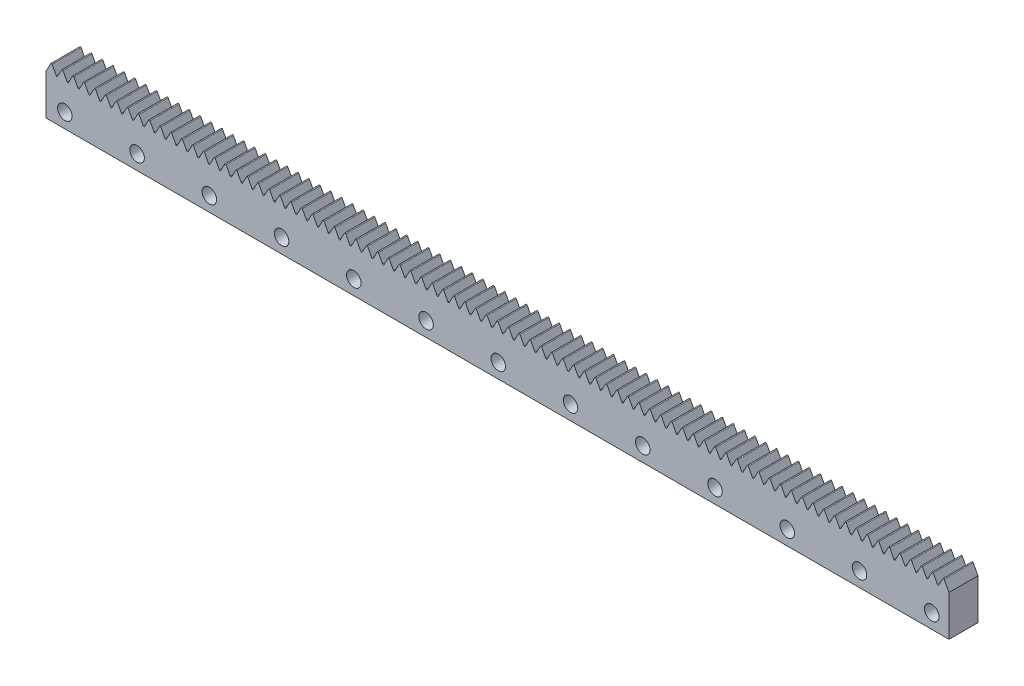
SolidWorks part; units mm, degrees
ref_plane "Front Plane" through (0, 0, 0) normal (0, 0, 1) x (1, 0, 0)
ref_plane "Top Plane" through (0, 0, 0) normal (0, 1, 0) x (1, 0, 0)
ref_plane "Right Plane" through (0, 0, 0) normal (1, 0, 0) x (0, 0, -1)
sketch "Sketch1" plane through (0, 0, 0) normal (0, 0, 1) x (1, 0, 0)
  line L0 (0, 0) -> (124.5, 0)
  line L1 (124.5, 0) -> (124.5, 5.6)
  line L2 (0, 0) -> (0, 5.6)
  line L19 (123.8381, 6.8355) -> (124.5, 5.6)
  line L20 (123.6619, 6.8355) -> (123.0881, 5.7645)
  line L21 (122.3381, 6.8355) -> (122.9119, 5.7645)
  line L22 (122.1619, 6.8355) -> (121.5881, 5.7645)
  line L23 (120.8381, 6.8355) -> (121.4119, 5.7645)
  line L24 (120.6619, 6.8355) -> (120.0881, 5.7645)
  line L25 (119.3381, 6.8355) -> (119.9119, 5.7645)
  line L26 (119.1619, 6.8355) -> (118.5881, 5.7645)
  line L27 (117.8381, 6.8355) -> (118.4119, 5.7645)
  line L28 (117.6619, 6.8355) -> (117.0881, 5.7645)
  line L29 (116.3381, 6.8355) -> (116.9119, 5.7645)
  line L30 (116.1619, 6.8355) -> (115.5881, 5.7645)
  line L31 (114.8381, 6.8355) -> (115.4119, 5.7645)
  line L32 (114.6619, 6.8355) -> (114.0881, 5.7645)
  line L33 (113.3381, 6.8355) -> (113.9119, 5.7645)
  line L34 (113.1619, 6.8355) -> (112.5881, 5.7645)
  line L35 (111.8381, 6.8355) -> (112.4119, 5.7645)
  line L36 (111.6619, 6.8355) -> (111.0881, 5.7645)
  line L37 (110.3381, 6.8355) -> (110.9119, 5.7645)
  line L38 (110.1619, 6.8355) -> (109.5881, 5.7645)
  line L39 (108.8381, 6.8355) -> (109.4119, 5.7645)
  line L40 (108.6619, 6.8355) -> (108.0881, 5.7645)
  line L41 (107.3381, 6.8355) -> (107.9119, 5.7645)
  line L42 (107.1619, 6.8355) -> (106.5881, 5.7645)
  line L43 (105.8381, 6.8355) -> (106.4119, 5.7645)
  line L44 (105.6619, 6.8355) -> (105.0881, 5.7645)
  line L45 (104.3381, 6.8355) -> (104.9119, 5.7645)
  line L46 (104.1619, 6.8355) -> (103.5881, 5.7645)
  line L47 (102.8381, 6.8355) -> (103.4119, 5.7645)
  line L48 (102.6619, 6.8355) -> (102.0881, 5.7645)
  line L49 (101.3381, 6.8355) -> (101.9119, 5.7645)
  line L50 (101.1619, 6.8355) -> (100.5881, 5.7645)
  line L51 (99.8381, 6.8355) -> (100.4119, 5.7645)
  line L52 (99.6619, 6.8355) -> (99.0881, 5.7645)
  line L53 (98.3381, 6.8355) -> (98.9119, 5.7645)
  line L54 (98.1619, 6.8355) -> (97.5881, 5.7645)
  line L55 (96.8381, 6.8355) -> (97.4119, 5.7645)
  line L56 (96.6619, 6.8355) -> (96.0881, 5.7645)
  line L57 (95.3381, 6.8355) -> (95.9119, 5.7645)
  line L58 (95.1619, 6.8355) -> (94.5881, 5.7645)
  line L59 (93.8381, 6.8355) -> (94.4119, 5.7645)
  line L60 (93.6619, 6.8355) -> (93.0881, 5.7645)
  line L61 (92.3381, 6.8355) -> (92.9119, 5.7645)
  line L62 (92.1619, 6.8355) -> (91.5881, 5.7645)
  line L63 (90.8381, 6.8355) -> (91.4119, 5.7645)
  line L64 (90.6619, 6.8355) -> (90.0881, 5.7645)
  line L65 (89.3381, 6.8355) -> (89.9119, 5.7645)
  line L66 (89.1619, 6.8355) -> (88.5881, 5.7645)
  line L67 (87.8381, 6.8355) -> (88.4119, 5.7645)
  line L68 (87.6619, 6.8355) -> (87.0881, 5.7645)
  line L69 (86.3381, 6.8355) -> (86.9119, 5.7645)
  line L70 (86.1619, 6.8355) -> (85.5881, 5.7645)
  line L71 (84.8381, 6.8355) -> (85.4119, 5.7645)
  line L72 (84.6619, 6.8355) -> (84.0881, 5.7645)
  line L73 (83.3381, 6.8355) -> (83.9119, 5.7645)
  line L74 (83.1619, 6.8355) -> (82.5881, 5.7645)
  line L75 (81.8381, 6.8355) -> (82.4119, 5.7645)
  line L76 (81.6619, 6.8355) -> (81.0881, 5.7645)
  line L77 (80.3381, 6.8355) -> (80.9119, 5.7645)
  line L78 (80.1619, 6.8355) -> (79.5881, 5.7645)
  line L79 (78.8381, 6.8355) -> (79.4119, 5.7645)
  line L80 (78.6619, 6.8355) -> (78.0881, 5.7645)
  line L81 (77.3381, 6.8355) -> (77.9119, 5.7645)
  line L82 (77.1619, 6.8355) -> (76.5881, 5.7645)
  line L83 (75.8381, 6.8355) -> (76.4119, 5.7645)
  line L84 (75.6619, 6.8355) -> (75.0881, 5.7645)
  line L85 (74.3381, 6.8355) -> (74.9119, 5.7645)
  line L86 (74.1619, 6.8355) -> (73.5881, 5.7645)
  line L87 (72.8381, 6.8355) -> (73.4119, 5.7645)
  line L88 (72.6619, 6.8355) -> (72.0881, 5.7645)
  line L89 (71.3381, 6.8355) -> (71.9119, 5.7645)
  line L90 (71.1619, 6.8355) -> (70.5881, 5.7645)
  line L91 (69.8381, 6.8355) -> (70.4119, 5.7645)
  line L92 (69.6619, 6.8355) -> (69.0881, 5.7645)
  line L93 (68.3381, 6.8355) -> (68.9119, 5.7645)
  line L94 (68.1619, 6.8355) -> (67.5881, 5.7645)
  line L95 (66.8381, 6.8355) -> (67.4119, 5.7645)
  line L96 (66.6619, 6.8355) -> (66.0881, 5.7645)
  line L97 (65.3381, 6.8355) -> (65.9119, 5.7645)
  line L98 (65.1619, 6.8355) -> (64.5881, 5.7645)
  line L99 (63.8381, 6.8355) -> (64.4119, 5.7645)
  line L100 (63.6619, 6.8355) -> (63.0881, 5.7645)
  line L101 (62.3381, 6.8355) -> (62.9119, 5.7645)
  line L102 (62.1619, 6.8355) -> (61.5881, 5.7645)
  line L103 (60.8381, 6.8355) -> (61.4119, 5.7645)
  line L104 (60.6619, 6.8355) -> (60.0881, 5.7645)
  line L105 (59.3381, 6.8355) -> (59.9119, 5.7645)
  line L106 (59.1619, 6.8355) -> (58.5881, 5.7645)
  line L107 (57.8381, 6.8355) -> (58.4119, 5.7645)
  line L108 (57.6619, 6.8355) -> (57.0881, 5.7645)
  line L109 (56.3381, 6.8355) -> (56.9119, 5.7645)
  line L110 (56.1619, 6.8355) -> (55.5881, 5.7645)
  line L111 (54.8381, 6.8355) -> (55.4119, 5.7645)
  line L112 (54.6619, 6.8355) -> (54.0881, 5.7645)
  line L113 (53.3381, 6.8355) -> (53.9119, 5.7645)
  line L114 (53.1619, 6.8355) -> (52.5881, 5.7645)
  line L115 (51.8381, 6.8355) -> (52.4119, 5.7645)
  line L116 (51.6619, 6.8355) -> (51.0881, 5.7645)
  line L117 (50.3381, 6.8355) -> (50.9119, 5.7645)
  line L118 (50.1619, 6.8355) -> (49.5881, 5.7645)
  line L119 (48.8381, 6.8355) -> (49.4119, 5.7645)
  line L120 (48.6619, 6.8355) -> (48.0881, 5.7645)
  line L121 (47.3381, 6.8355) -> (47.9119, 5.7645)
  line L122 (47.1619, 6.8355) -> (46.5881, 5.7645)
  line L123 (45.8381, 6.8355) -> (46.4119, 5.7645)
  line L124 (45.6619, 6.8355) -> (45.0881, 5.7645)
  line L125 (44.3381, 6.8355) -> (44.9119, 5.7645)
  line L126 (44.1619, 6.8355) -> (43.5881, 5.7645)
  line L127 (42.8381, 6.8355) -> (43.4119, 5.7645)
  line L128 (42.6619, 6.8355) -> (42.0881, 5.7645)
  line L129 (41.3381, 6.8355) -> (41.9119, 5.7645)
  line L130 (41.1619, 6.8355) -> (40.5881, 5.7645)
  line L131 (39.8381, 6.8355) -> (40.4119, 5.7645)
  line L132 (39.6619, 6.8355) -> (39.0881, 5.7645)
  line L133 (38.3381, 6.8355) -> (38.9119, 5.7645)
  line L134 (38.1619, 6.8355) -> (37.5881, 5.7645)
  line L135 (36.8381, 6.8355) -> (37.4119, 5.7645)
  line L136 (36.6619, 6.8355) -> (36.0881, 5.7645)
  line L137 (35.3381, 6.8355) -> (35.9119, 5.7645)
  line L138 (35.1619, 6.8355) -> (34.5881, 5.7645)
  line L139 (33.8381, 6.8355) -> (34.4119, 5.7645)
  line L140 (33.6619, 6.8355) -> (33.0881, 5.7645)
  line L141 (32.3381, 6.8355) -> (32.9119, 5.7645)
  line L142 (32.1619, 6.8355) -> (31.5881, 5.7645)
  line L143 (30.8381, 6.8355) -> (31.4119, 5.7645)
  line L144 (30.6619, 6.8355) -> (30.0881, 5.7645)
  line L145 (29.3381, 6.8355) -> (29.9119, 5.7645)
  line L146 (29.1619, 6.8355) -> (28.5881, 5.7645)
  line L147 (27.8381, 6.8355) -> (28.4119, 5.7645)
  line L148 (27.6619, 6.8355) -> (27.0881, 5.7645)
  line L149 (26.3381, 6.8355) -> (26.9119, 5.7645)
  line L150 (26.1619, 6.8355) -> (25.5881, 5.7645)
  line L151 (24.8381, 6.8355) -> (25.4119, 5.7645)
  line L152 (24.6619, 6.8355) -> (24.0881, 5.7645)
  line L153 (23.3381, 6.8355) -> (23.9119, 5.7645)
  line L154 (23.1619, 6.8355) -> (22.5881, 5.7645)
  line L155 (21.8381, 6.8355) -> (22.4119, 5.7645)
  line L156 (21.6619, 6.8355) -> (21.0881, 5.7645)
  line L157 (20.3381, 6.8355) -> (20.9119, 5.7645)
  line L158 (20.1619, 6.8355) -> (19.5881, 5.7645)
  line L159 (18.8381, 6.8355) -> (19.4119, 5.7645)
  line L160 (18.6619, 6.8355) -> (18.0881, 5.7645)
  line L161 (17.3381, 6.8355) -> (17.9119, 5.7645)
  line L162 (17.1619, 6.8355) -> (16.5881, 5.7645)
  line L163 (15.8381, 6.8355) -> (16.4119, 5.7645)
  line L164 (15.6619, 6.8355) -> (15.0881, 5.7645)
  line L165 (14.3381, 6.8355) -> (14.9119, 5.7645)
  line L166 (14.1619, 6.8355) -> (13.5881, 5.7645)
  line L167 (12.8381, 6.8355) -> (13.4119, 5.7645)
  line L168 (12.6619, 6.8355) -> (12.0881, 5.7645)
  line L169 (11.3381, 6.8355) -> (11.9119, 5.7645)
  line L170 (11.1619, 6.8355) -> (10.5881, 5.7645)
  line L171 (9.8381, 6.8355) -> (10.4119, 5.7645)
  line L172 (9.6619, 6.8355) -> (9.0881, 5.7645)
  line L173 (8.3381, 6.8355) -> (8.9119, 5.7645)
  line L174 (8.1619, 6.8355) -> (7.5881, 5.7645)
  line L175 (6.8381, 6.8355) -> (7.4119, 5.7645)
  line L176 (6.6619, 6.8355) -> (6.0881, 5.7645)
  line L177 (5.3381, 6.8355) -> (5.9119, 5.7645)
  line L178 (5.1619, 6.8355) -> (4.5881, 5.7645)
  line L179 (3.8381, 6.8355) -> (4.4119, 5.7645)
  line L180 (3.6619, 6.8355) -> (3.0881, 5.7645)
  line L181 (2.3381, 6.8355) -> (2.9119, 5.7645)
  line L182 (2.1619, 6.8355) -> (1.5881, 5.7645)
  line L183 (0.8381, 6.8355) -> (1.4119, 5.7645)
  line L184 (0.6619, 6.8355) -> (0, 5.6)
  arc A0 (122.9119, 5.7645) -> (123.0881, 5.7645) centre (123, 5.8118) ccw
  arc A1 (123.8381, 6.8355) -> (123.6619, 6.8355) centre (123.75, 6.7882) ccw
  arc A2 (121.4119, 5.7645) -> (121.5881, 5.7645) centre (121.5, 5.8118) ccw
  arc A3 (122.3381, 6.8355) -> (122.1619, 6.8355) centre (122.25, 6.7882) ccw
  arc A4 (119.9119, 5.7645) -> (120.0881, 5.7645) centre (120, 5.8118) ccw
  arc A5 (120.8381, 6.8355) -> (120.6619, 6.8355) centre (120.75, 6.7882) ccw
  arc A6 (118.4119, 5.7645) -> (118.5881, 5.7645) centre (118.5, 5.8118) ccw
  arc A7 (119.3381, 6.8355) -> (119.1619, 6.8355) centre (119.25, 6.7882) ccw
  arc A8 (116.9119, 5.7645) -> (117.0881, 5.7645) centre (117, 5.8118) ccw
  arc A9 (117.8381, 6.8355) -> (117.6619, 6.8355) centre (117.75, 6.7882) ccw
  arc A10 (115.4119, 5.7645) -> (115.5881, 5.7645) centre (115.5, 5.8118) ccw
  arc A11 (116.3381, 6.8355) -> (116.1619, 6.8355) centre (116.25, 6.7882) ccw
  arc A12 (113.9119, 5.7645) -> (114.0881, 5.7645) centre (114, 5.8118) ccw
  arc A13 (114.8381, 6.8355) -> (114.6619, 6.8355) centre (114.75, 6.7882) ccw
  arc A14 (112.4119, 5.7645) -> (112.5881, 5.7645) centre (112.5, 5.8118) ccw
  arc A15 (113.3381, 6.8355) -> (113.1619, 6.8355) centre (113.25, 6.7882) ccw
  arc A16 (110.9119, 5.7645) -> (111.0881, 5.7645) centre (111, 5.8118) ccw
  arc A17 (111.8381, 6.8355) -> (111.6619, 6.8355) centre (111.75, 6.7882) ccw
  arc A18 (109.4119, 5.7645) -> (109.5881, 5.7645) centre (109.5, 5.8118) ccw
  arc A19 (110.3381, 6.8355) -> (110.1619, 6.8355) centre (110.25, 6.7882) ccw
  arc A20 (107.9119, 5.7645) -> (108.0881, 5.7645) centre (108, 5.8118) ccw
  arc A21 (108.8381, 6.8355) -> (108.6619, 6.8355) centre (108.75, 6.7882) ccw
  arc A22 (106.4119, 5.7645) -> (106.5881, 5.7645) centre (106.5, 5.8118) ccw
  arc A23 (107.3381, 6.8355) -> (107.1619, 6.8355) centre (107.25, 6.7882) ccw
  arc A24 (104.9119, 5.7645) -> (105.0881, 5.7645) centre (105, 5.8118) ccw
  arc A25 (105.8381, 6.8355) -> (105.6619, 6.8355) centre (105.75, 6.7882) ccw
  arc A26 (103.4119, 5.7645) -> (103.5881, 5.7645) centre (103.5, 5.8118) ccw
  arc A27 (104.3381, 6.8355) -> (104.1619, 6.8355) centre (104.25, 6.7882) ccw
  arc A28 (101.9119, 5.7645) -> (102.0881, 5.7645) centre (102, 5.8118) ccw
  arc A29 (102.8381, 6.8355) -> (102.6619, 6.8355) centre (102.75, 6.7882) ccw
  arc A30 (100.4119, 5.7645) -> (100.5881, 5.7645) centre (100.5, 5.8118) ccw
  arc A31 (101.3381, 6.8355) -> (101.1619, 6.8355) centre (101.25, 6.7882) ccw
  arc A32 (98.9119, 5.7645) -> (99.0881, 5.7645) centre (99, 5.8118) ccw
  arc A33 (99.8381, 6.8355) -> (99.6619, 6.8355) centre (99.75, 6.7882) ccw
  arc A34 (97.4119, 5.7645) -> (97.5881, 5.7645) centre (97.5, 5.8118) ccw
  arc A35 (98.3381, 6.8355) -> (98.1619, 6.8355) centre (98.25, 6.7882) ccw
  arc A36 (95.9119, 5.7645) -> (96.0881, 5.7645) centre (96, 5.8118) ccw
  arc A37 (96.8381, 6.8355) -> (96.6619, 6.8355) centre (96.75, 6.7882) ccw
  arc A38 (94.4119, 5.7645) -> (94.5881, 5.7645) centre (94.5, 5.8118) ccw
  arc A39 (95.3381, 6.8355) -> (95.1619, 6.8355) centre (95.25, 6.7882) ccw
  arc A40 (92.9119, 5.7645) -> (93.0881, 5.7645) centre (93, 5.8118) ccw
  arc A41 (93.8381, 6.8355) -> (93.6619, 6.8355) centre (93.75, 6.7882) ccw
  arc A42 (91.4119, 5.7645) -> (91.5881, 5.7645) centre (91.5, 5.8118) ccw
  arc A43 (92.3381, 6.8355) -> (92.1619, 6.8355) centre (92.25, 6.7882) ccw
  arc A44 (89.9119, 5.7645) -> (90.0881, 5.7645) centre (90, 5.8118) ccw
  arc A45 (90.8381, 6.8355) -> (90.6619, 6.8355) centre (90.75, 6.7882) ccw
  arc A46 (88.4119, 5.7645) -> (88.5881, 5.7645) centre (88.5, 5.8118) ccw
  arc A47 (89.3381, 6.8355) -> (89.1619, 6.8355) centre (89.25, 6.7882) ccw
  arc A48 (86.9119, 5.7645) -> (87.0881, 5.7645) centre (87, 5.8118) ccw
  arc A49 (87.8381, 6.8355) -> (87.6619, 6.8355) centre (87.75, 6.7882) ccw
  arc A50 (85.4119, 5.7645) -> (85.5881, 5.7645) centre (85.5, 5.8118) ccw
  arc A51 (86.3381, 6.8355) -> (86.1619, 6.8355) centre (86.25, 6.7882) ccw
  arc A52 (83.9119, 5.7645) -> (84.0881, 5.7645) centre (84, 5.8118) ccw
  arc A53 (84.8381, 6.8355) -> (84.6619, 6.8355) centre (84.75, 6.7882) ccw
  arc A54 (82.4119, 5.7645) -> (82.5881, 5.7645) centre (82.5, 5.8118) ccw
  arc A55 (83.3381, 6.8355) -> (83.1619, 6.8355) centre (83.25, 6.7882) ccw
  arc A56 (80.9119, 5.7645) -> (81.0881, 5.7645) centre (81, 5.8118) ccw
  arc A57 (81.8381, 6.8355) -> (81.6619, 6.8355) centre (81.75, 6.7882) ccw
  arc A58 (79.4119, 5.7645) -> (79.5881, 5.7645) centre (79.5, 5.8118) ccw
  arc A59 (80.3381, 6.8355) -> (80.1619, 6.8355) centre (80.25, 6.7882) ccw
  arc A60 (77.9119, 5.7645) -> (78.0881, 5.7645) centre (78, 5.8118) ccw
  arc A61 (78.8381, 6.8355) -> (78.6619, 6.8355) centre (78.75, 6.7882) ccw
  arc A62 (76.4119, 5.7645) -> (76.5881, 5.7645) centre (76.5, 5.8118) ccw
  arc A63 (77.3381, 6.8355) -> (77.1619, 6.8355) centre (77.25, 6.7882) ccw
  arc A64 (74.9119, 5.7645) -> (75.0881, 5.7645) centre (75, 5.8118) ccw
  arc A65 (75.8381, 6.8355) -> (75.6619, 6.8355) centre (75.75, 6.7882) ccw
  arc A66 (73.4119, 5.7645) -> (73.5881, 5.7645) centre (73.5, 5.8118) ccw
  arc A67 (74.3381, 6.8355) -> (74.1619, 6.8355) centre (74.25, 6.7882) ccw
  arc A68 (71.9119, 5.7645) -> (72.0881, 5.7645) centre (72, 5.8118) ccw
  arc A69 (72.8381, 6.8355) -> (72.6619, 6.8355) centre (72.75, 6.7882) ccw
  arc A70 (70.4119, 5.7645) -> (70.5881, 5.7645) centre (70.5, 5.8118) ccw
  arc A71 (71.3381, 6.8355) -> (71.1619, 6.8355) centre (71.25, 6.7882) ccw
  arc A72 (68.9119, 5.7645) -> (69.0881, 5.7645) centre (69, 5.8118) ccw
  arc A73 (69.8381, 6.8355) -> (69.6619, 6.8355) centre (69.75, 6.7882) ccw
  arc A74 (67.4119, 5.7645) -> (67.5881, 5.7645) centre (67.5, 5.8118) ccw
  arc A75 (68.3381, 6.8355) -> (68.1619, 6.8355) centre (68.25, 6.7882) ccw
  arc A76 (65.9119, 5.7645) -> (66.0881, 5.7645) centre (66, 5.8118) ccw
  arc A77 (66.8381, 6.8355) -> (66.6619, 6.8355) centre (66.75, 6.7882) ccw
  arc A78 (64.4119, 5.7645) -> (64.5881, 5.7645) centre (64.5, 5.8118) ccw
  arc A79 (65.3381, 6.8355) -> (65.1619, 6.8355) centre (65.25, 6.7882) ccw
  arc A80 (62.9119, 5.7645) -> (63.0881, 5.7645) centre (63, 5.8118) ccw
  arc A81 (63.8381, 6.8355) -> (63.6619, 6.8355) centre (63.75, 6.7882) ccw
  arc A82 (61.4119, 5.7645) -> (61.5881, 5.7645) centre (61.5, 5.8118) ccw
  arc A83 (62.3381, 6.8355) -> (62.1619, 6.8355) centre (62.25, 6.7882) ccw
  arc A84 (59.9119, 5.7645) -> (60.0881, 5.7645) centre (60, 5.8118) ccw
  arc A85 (60.8381, 6.8355) -> (60.6619, 6.8355) centre (60.75, 6.7882) ccw
  arc A86 (58.4119, 5.7645) -> (58.5881, 5.7645) centre (58.5, 5.8118) ccw
  arc A87 (59.3381, 6.8355) -> (59.1619, 6.8355) centre (59.25, 6.7882) ccw
  arc A88 (56.9119, 5.7645) -> (57.0881, 5.7645) centre (57, 5.8118) ccw
  arc A89 (57.8381, 6.8355) -> (57.6619, 6.8355) centre (57.75, 6.7882) ccw
  arc A90 (55.4119, 5.7645) -> (55.5881, 5.7645) centre (55.5, 5.8118) ccw
  arc A91 (56.3381, 6.8355) -> (56.1619, 6.8355) centre (56.25, 6.7882) ccw
  arc A92 (53.9119, 5.7645) -> (54.0881, 5.7645) centre (54, 5.8118) ccw
  arc A93 (54.8381, 6.8355) -> (54.6619, 6.8355) centre (54.75, 6.7882) ccw
  arc A94 (52.4119, 5.7645) -> (52.5881, 5.7645) centre (52.5, 5.8118) ccw
  arc A95 (53.3381, 6.8355) -> (53.1619, 6.8355) centre (53.25, 6.7882) ccw
  arc A96 (50.9119, 5.7645) -> (51.0881, 5.7645) centre (51, 5.8118) ccw
  arc A97 (51.8381, 6.8355) -> (51.6619, 6.8355) centre (51.75, 6.7882) ccw
  arc A98 (49.4119, 5.7645) -> (49.5881, 5.7645) centre (49.5, 5.8118) ccw
  arc A99 (50.3381, 6.8355) -> (50.1619, 6.8355) centre (50.25, 6.7882) ccw
  arc A100 (47.9119, 5.7645) -> (48.0881, 5.7645) centre (48, 5.8118) ccw
  arc A101 (48.8381, 6.8355) -> (48.6619, 6.8355) centre (48.75, 6.7882) ccw
  arc A102 (46.4119, 5.7645) -> (46.5881, 5.7645) centre (46.5, 5.8118) ccw
  arc A103 (47.3381, 6.8355) -> (47.1619, 6.8355) centre (47.25, 6.7882) ccw
  arc A104 (44.9119, 5.7645) -> (45.0881, 5.7645) centre (45, 5.8118) ccw
  arc A105 (45.8381, 6.8355) -> (45.6619, 6.8355) centre (45.75, 6.7882) ccw
  arc A106 (43.4119, 5.7645) -> (43.5881, 5.7645) centre (43.5, 5.8118) ccw
  arc A107 (44.3381, 6.8355) -> (44.1619, 6.8355) centre (44.25, 6.7882) ccw
  arc A108 (41.9119, 5.7645) -> (42.0881, 5.7645) centre (42, 5.8118) ccw
  arc A109 (42.8381, 6.8355) -> (42.6619, 6.8355) centre (42.75, 6.7882) ccw
  arc A110 (40.4119, 5.7645) -> (40.5881, 5.7645) centre (40.5, 5.8118) ccw
  arc A111 (41.3381, 6.8355) -> (41.1619, 6.8355) centre (41.25, 6.7882) ccw
  arc A112 (38.9119, 5.7645) -> (39.0881, 5.7645) centre (39, 5.8118) ccw
  arc A113 (39.8381, 6.8355) -> (39.6619, 6.8355) centre (39.75, 6.7882) ccw
  arc A114 (37.4119, 5.7645) -> (37.5881, 5.7645) centre (37.5, 5.8118) ccw
  arc A115 (38.3381, 6.8355) -> (38.1619, 6.8355) centre (38.25, 6.7882) ccw
  arc A116 (35.9119, 5.7645) -> (36.0881, 5.7645) centre (36, 5.8118) ccw
  arc A117 (36.8381, 6.8355) -> (36.6619, 6.8355) centre (36.75, 6.7882) ccw
  arc A118 (34.4119, 5.7645) -> (34.5881, 5.7645) centre (34.5, 5.8118) ccw
  arc A119 (35.3381, 6.8355) -> (35.1619, 6.8355) centre (35.25, 6.7882) ccw
  arc A120 (32.9119, 5.7645) -> (33.0881, 5.7645) centre (33, 5.8118) ccw
  arc A121 (33.8381, 6.8355) -> (33.6619, 6.8355) centre (33.75, 6.7882) ccw
  arc A122 (31.4119, 5.7645) -> (31.5881, 5.7645) centre (31.5, 5.8118) ccw
  arc A123 (32.3381, 6.8355) -> (32.1619, 6.8355) centre (32.25, 6.7882) ccw
  arc A124 (29.9119, 5.7645) -> (30.0881, 5.7645) centre (30, 5.8118) ccw
  arc A125 (30.8381, 6.8355) -> (30.6619, 6.8355) centre (30.75, 6.7882) ccw
  arc A126 (28.4119, 5.7645) -> (28.5881, 5.7645) centre (28.5, 5.8118) ccw
  arc A127 (29.3381, 6.8355) -> (29.1619, 6.8355) centre (29.25, 6.7882) ccw
  arc A128 (26.9119, 5.7645) -> (27.0881, 5.7645) centre (27, 5.8118) ccw
  arc A129 (27.8381, 6.8355) -> (27.6619, 6.8355) centre (27.75, 6.7882) ccw
  arc A130 (25.4119, 5.7645) -> (25.5881, 5.7645) centre (25.5, 5.8118) ccw
  arc A131 (26.3381, 6.8355) -> (26.1619, 6.8355) centre (26.25, 6.7882) ccw
  arc A132 (23.9119, 5.7645) -> (24.0881, 5.7645) centre (24, 5.8118) ccw
  arc A133 (24.8381, 6.8355) -> (24.6619, 6.8355) centre (24.75, 6.7882) ccw
  arc A134 (22.4119, 5.7645) -> (22.5881, 5.7645) centre (22.5, 5.8118) ccw
  arc A135 (23.3381, 6.8355) -> (23.1619, 6.8355) centre (23.25, 6.7882) ccw
  arc A136 (20.9119, 5.7645) -> (21.0881, 5.7645) centre (21, 5.8118) ccw
  arc A137 (21.8381, 6.8355) -> (21.6619, 6.8355) centre (21.75, 6.7882) ccw
  arc A138 (19.4119, 5.7645) -> (19.5881, 5.7645) centre (19.5, 5.8118) ccw
  arc A139 (20.3381, 6.8355) -> (20.1619, 6.8355) centre (20.25, 6.7882) ccw
  arc A140 (17.9119, 5.7645) -> (18.0881, 5.7645) centre (18, 5.8118) ccw
  arc A141 (18.8381, 6.8355) -> (18.6619, 6.8355) centre (18.75, 6.7882) ccw
  arc A142 (16.4119, 5.7645) -> (16.5881, 5.7645) centre (16.5, 5.8118) ccw
  arc A143 (17.3381, 6.8355) -> (17.1619, 6.8355) centre (17.25, 6.7882) ccw
  arc A144 (14.9119, 5.7645) -> (15.0881, 5.7645) centre (15, 5.8118) ccw
  arc A145 (15.8381, 6.8355) -> (15.6619, 6.8355) centre (15.75, 6.7882) ccw
  arc A146 (13.4119, 5.7645) -> (13.5881, 5.7645) centre (13.5, 5.8118) ccw
  arc A147 (14.3381, 6.8355) -> (14.1619, 6.8355) centre (14.25, 6.7882) ccw
  arc A148 (11.9119, 5.7645) -> (12.0881, 5.7645) centre (12, 5.8118) ccw
  arc A149 (12.8381, 6.8355) -> (12.6619, 6.8355) centre (12.75, 6.7882) ccw
  arc A150 (10.4119, 5.7645) -> (10.5881, 5.7645) centre (10.5, 5.8118) ccw
  arc A151 (11.3381, 6.8355) -> (11.1619, 6.8355) centre (11.25, 6.7882) ccw
  arc A152 (8.9119, 5.7645) -> (9.0881, 5.7645) centre (9, 5.8118) ccw
  arc A153 (9.8381, 6.8355) -> (9.6619, 6.8355) centre (9.75, 6.7882) ccw
  arc A154 (7.4119, 5.7645) -> (7.5881, 5.7645) centre (7.5, 5.8118) ccw
  arc A155 (8.3381, 6.8355) -> (8.1619, 6.8355) centre (8.25, 6.7882) ccw
  arc A156 (5.9119, 5.7645) -> (6.0881, 5.7645) centre (6, 5.8118) ccw
  arc A157 (6.8381, 6.8355) -> (6.6619, 6.8355) centre (6.75, 6.7882) ccw
  arc A158 (4.4119, 5.7645) -> (4.5881, 5.7645) centre (4.5, 5.8118) ccw
  arc A159 (5.3381, 6.8355) -> (5.1619, 6.8355) centre (5.25, 6.7882) ccw
  arc A160 (2.9119, 5.7645) -> (3.0881, 5.7645) centre (3, 5.8118) ccw
  arc A161 (3.8381, 6.8355) -> (3.6619, 6.8355) centre (3.75, 6.7882) ccw
  arc A162 (1.4119, 5.7645) -> (1.5881, 5.7645) centre (1.5, 5.8118) ccw
  arc A163 (2.3381, 6.8355) -> (2.1619, 6.8355) centre (2.25, 6.7882) ccw
  arc A165 (0.8381, 6.8355) -> (0.6619, 6.8355) centre (0.75, 6.7882) ccw
  point P9 (0, 0)
  point P15 (0, 0)
  point P22 (0, 0)
  point P29 (0, 5.6177)
  dimension "D3" = 0.1
  dimension "D1" = 124.5
  dimension "D2" = 5.6
extrude "Boss-Extrude1" add sketch "Sketch1" along normal blind 4
sketch "Sketch2" plane through (0, 0, 4) normal (0, 0, 1) x (1, 0, 0)
  line L0 (0, 0) -> (124.5, 0) construction
  line L1 (0, 5.6) -> (0, 0) construction
  circle A0 centre (2.6, 2) radius 1
  circle A1 centre (12.56, 2) radius 1
  circle A2 centre (22.52, 2) radius 1
  circle A3 centre (32.48, 2) radius 1
  circle A4 centre (42.44, 2) radius 1
  circle A5 centre (52.4, 2) radius 1
  circle A6 centre (62.36, 2) radius 1
  circle A7 centre (72.32, 2) radius 1
  circle A8 centre (82.28, 2) radius 1
  circle A9 centre (92.24, 2) radius 1
  circle A10 centre (102.2, 2) radius 1
  circle A11 centre (112.16, 2) radius 1
  circle A12 centre (122.12, 2) radius 1
  dimension "D1" = 2
  dimension "D2" = 2
  dimension "D3" = 2.6
  dimension "D4" = 13
extrude "Cut-Extrude1" cut sketch "Sketch2" against normal through all
